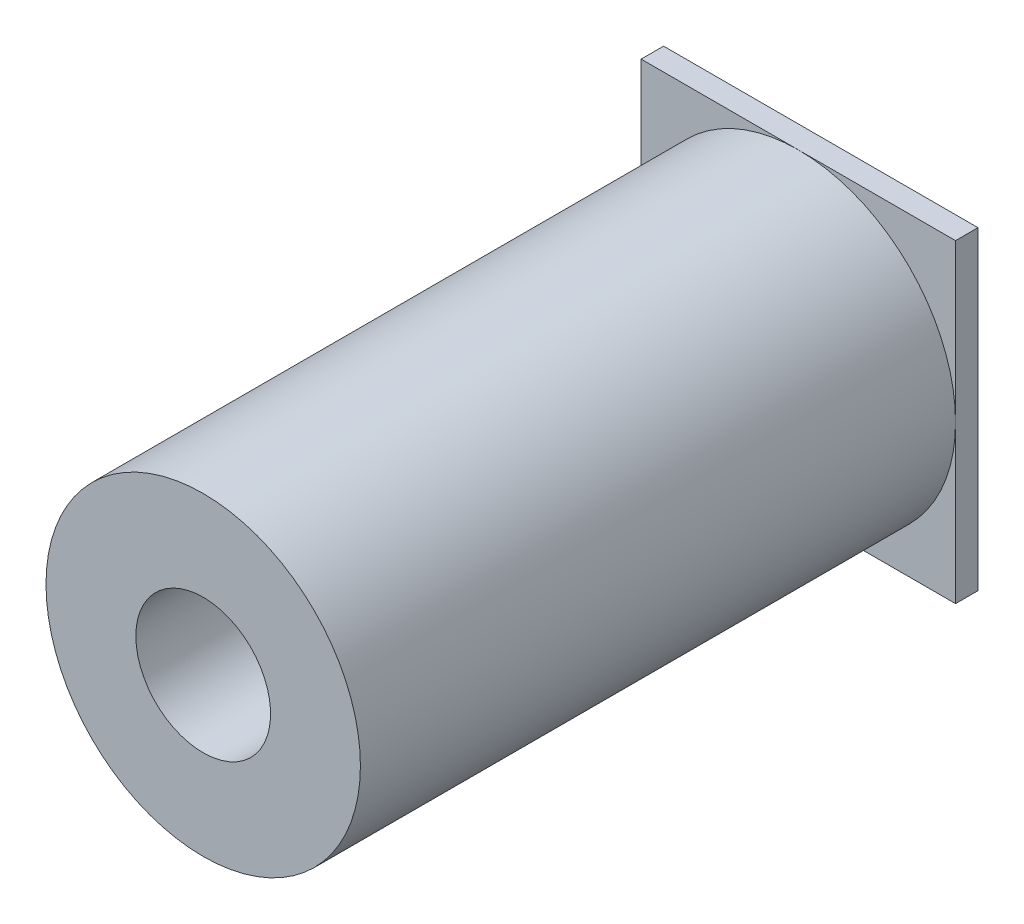
SolidWorks part; units mm, degrees
ref_plane "Front Plane" through (0, 0, 0) normal (0, 0, 1) x (1, 0, 0)
ref_plane "Top Plane" through (0, 0, 0) normal (0, 1, 0) x (1, 0, 0)
ref_plane "Right Plane" through (0, 0, 0) normal (1, 0, 0) x (0, 0, -1)
sketch "Sketch1" plane through (0, 0, 0) normal (0, 0, 1) x (1, 0, 0)
  line L1 (-14, 14) -> (14, 14)
  line L2 (-14, 14) -> (-14, -14)
  line L3 (-14, -14) -> (14, -14)
  line L4 (14, 14) -> (14, -14)
  line L5 (-14, 14) -> (14, -14) construction
  line L6 (-14, -14) -> (14, 14) construction
  point P0 (0, 0)
  dimension "D1" = 28
extrude "Boss-Extrude1" add sketch "Sketch1" along normal blind 2
sketch "Sketch2" plane through (0, 0, 2) normal (0, 0, 1) x (1, 0, 0)
  circle A0 centre (0, 0) radius 14
  dimension "D1" = 28
extrude "Boss-Extrude2" add sketch "Sketch2" along normal blind 53
sketch "Sketch3" plane through (0, 0, 0) normal (0, 0, -1) x (-1, 0, 0)
  circle A0 centre (0, 0) radius 6
  dimension "D1" = 12
extrude "Cut-Extrude1" cut sketch "Sketch3" against normal through all
